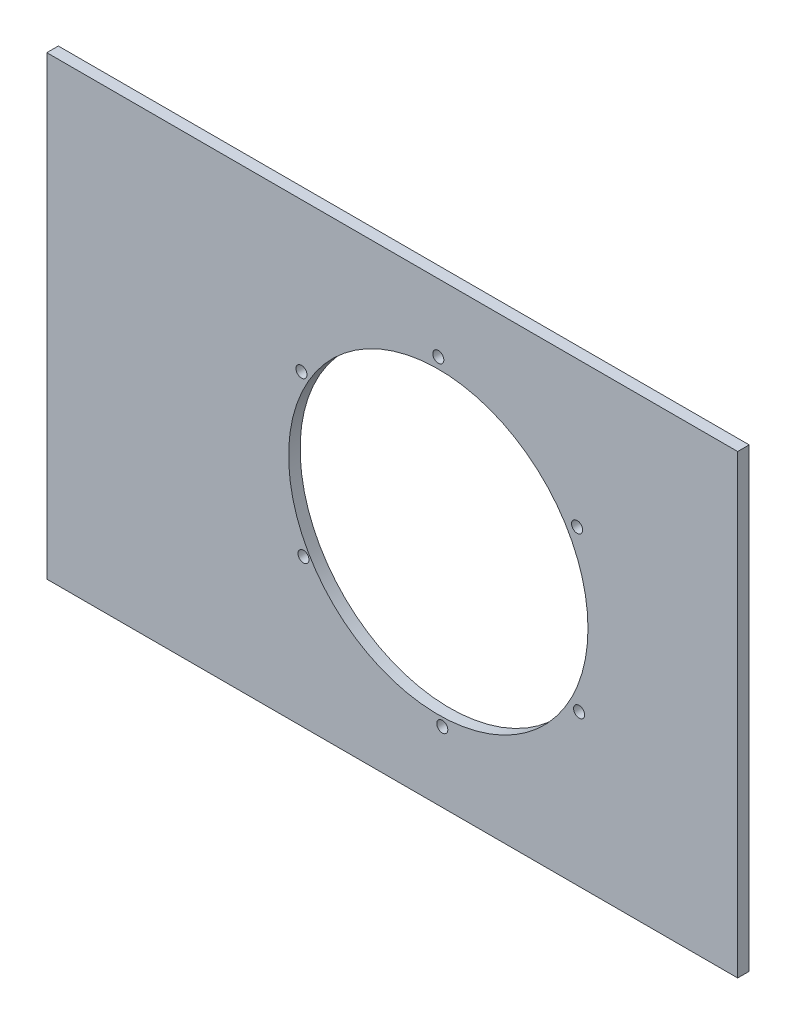
SolidWorks part; units mm, degrees
ref_plane "Front Plane" through (0, 0, 0) normal (0, 0, 1) x (1, 0, 0)
ref_plane "Top Plane" through (0, 0, 0) normal (0, 1, 0) x (1, 0, 0)
ref_plane "Right Plane" through (0, 0, 0) normal (1, 0, 0) x (0, 0, -1)
sketch "Sketch1" plane through (0, 0, 0) normal (0, 0, 1) x (1, 0, 0)
  line L0 (0, 125.73) -> (-24.3637, 125.73) construction
  line L1 (0, 0) -> (-381, 0)
  line L2 (0, 0) -> (0, 251.46)
  line L3 (0, 251.46) -> (-381, 251.46)
  line L4 (-381, 0) -> (-381, 251.46)
  circle A0 centre (-165.1, 125.73) radius 82.55
  circle A1 centre (-165.1, 214.122) radius 3.048
  circle A2 centre (-88.5503, 171.196) radius 3.048
  circle A3 centre (-87.4504, 83.439) radius 3.048
  circle A4 centre (-162.9003, 38.608) radius 3.048
  circle A5 centre (-239.45, 81.534) radius 3.048
  circle A6 centre (-240.5499, 169.291) radius 3.048
  point P24 (-164.0001, 126.365)
  dimension "D3" = 165.1
  dimension "D4" = 165.1
  dimension "D5" = 6.096
  dimension "D6" = 88.392
  dimension "D1" = 251.46
  dimension "D2" = 381
  dimension "5" = 125.73
  dimension "D7" = 6
extrude "Boss-Extrude1" add sketch "Sketch1" along normal blind 6.35
